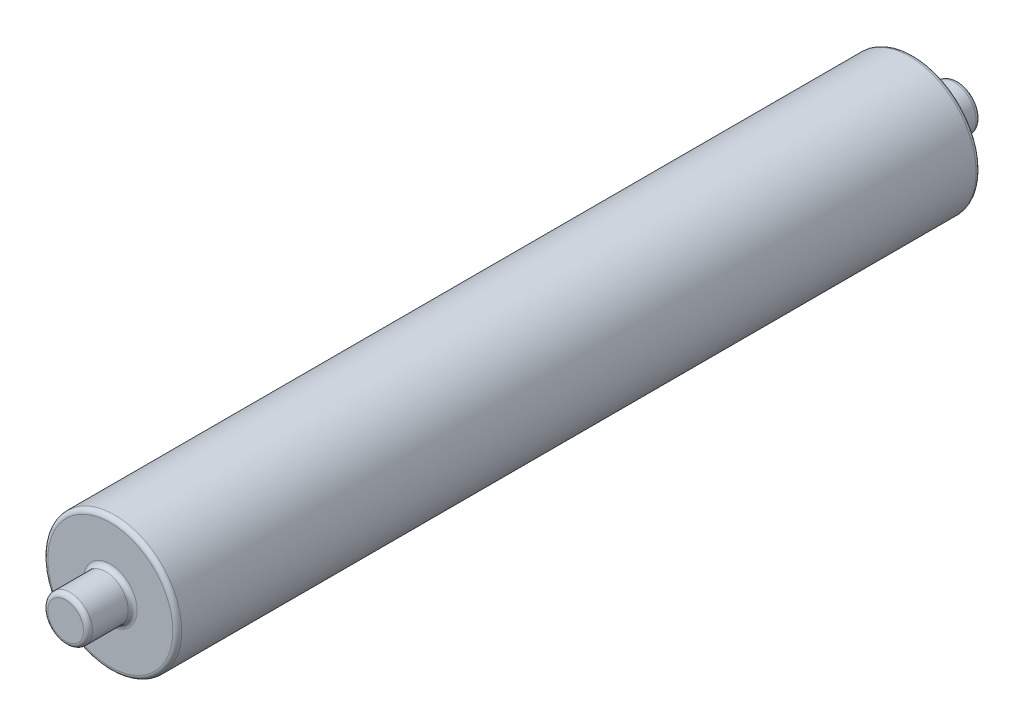
SolidWorks part; units mm, degrees
ref_plane "Front Plane" through (0, 0, 0) normal (0, 0, 1) x (1, 0, 0)
ref_plane "Top Plane" through (0, 0, 0) normal (0, 1, 0) x (1, 0, 0)
ref_plane "Right Plane" through (0, 0, 0) normal (1, 0, 0) x (0, 0, -1)
sketch "Sketch1" plane through (0, 0, 0) normal (0, 0, 1) x (1, 0, 0)
  circle A0 centre (0, 0) radius 38.1
  dimension "D1" = 76.2
extrude "Boss-Extrude1" add sketch "Sketch1" along normal blind 457.2
sketch "Sketch2" plane through (0, 0, 0) normal (0, 0, -1) x (-1, 0, 0)
  circle A0 centre (0, 0) radius 12.7
  dimension "D1" = 25.4
extrude "Boss-Extrude2" add sketch "Sketch2" along normal blind 25.4
sketch "Sketch3" plane through (0, 0, 457.2) normal (0, 0, 1) x (1, 0, 0)
  circle A0 centre (0, 0) radius 12.7
  dimension "D1" = 25.4
extrude "Boss-Extrude3" add sketch "Sketch3" along normal blind 25.4
fillet "Fillet1" radius 2.54 2 edges at (-12.7, 0, 0) (12.7, 0, 457.2)
fillet "Fillet2" radius 2.54 4 edges at (12.7, 0, 482.6) (-12.7, 0, -25.4) (38.1, 0, 0) (38.1, 0, 457.2)
